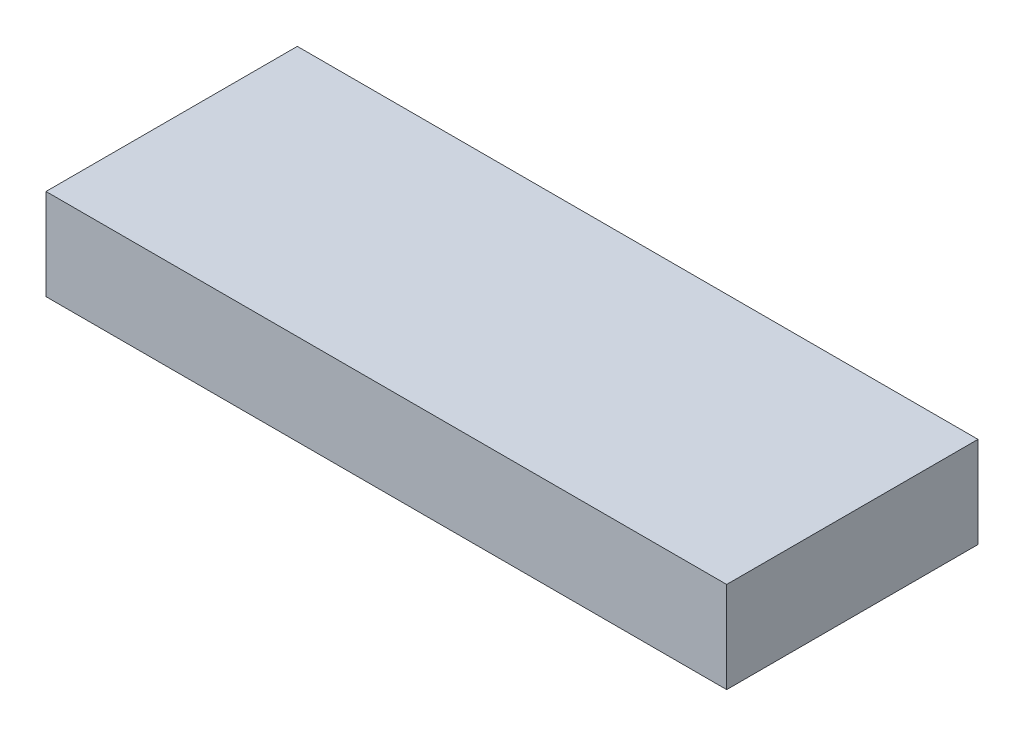
SolidWorks part; units mm, degrees
ref_plane "Front Plane" through (0, 0, 0) normal (0, 0, 1) x (1, 0, 0)
ref_plane "Top Plane" through (0, 0, 0) normal (0, 1, 0) x (1, 0, 0)
ref_plane "Right Plane" through (0, 0, 0) normal (1, 0, 0) x (0, 0, -1)
sketch "Sketch1" plane through (0, 0, 0) normal (0, 1, 0) x (1, 0, 0)
  line L1 (-16.25, 6) -> (16.25, 6)
  line L2 (-16.25, 6) -> (-16.25, -6)
  line L3 (-16.25, -6) -> (16.25, -6)
  line L4 (16.25, 6) -> (16.25, -6)
  line L5 (-16.25, 6) -> (16.25, -6) construction
  line L6 (-16.25, -6) -> (16.25, 6) construction
  point P0 (0, 0)
  dimension "D1" = 12
  dimension "D2" = 32.5
extrude "Boss-Extrude1" add sketch "Sketch1" along normal blind 4.35
